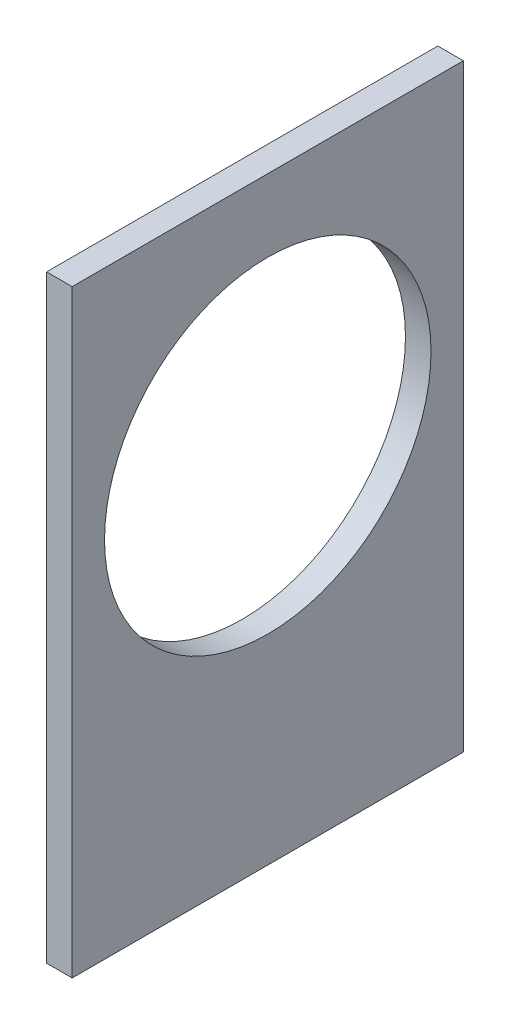
SolidWorks part; units mm, degrees
ref_plane "Front Plane" through (0, 0, 0) normal (0, 0, 1) x (1, 0, 0)
ref_plane "Top Plane" through (0, 0, 0) normal (0, 1, 0) x (1, 0, 0)
ref_plane "Right Plane" through (0, 0, 0) normal (1, 0, 0) x (0, 0, -1)
sketch "Sketch1" plane through (0, 0, 0) normal (1, 0, 0) x (0, 0, -1)
  line L1 (0, 0) -> (49, 0)
  line L2 (0, 0) -> (0, 75)
  line L3 (0, 75) -> (49, 75)
  line L4 (49, 0) -> (49, 75)
  dimension "D1" = 49
  dimension "D2" = 75
extrude "Boss-Extrude1" add sketch "Sketch1" along normal blind 3.2
sketch "Sketch2" plane through (3.2, 0, 0) normal (1, 0, 0) x (0, 0, -1)
  line L0 (24.5, 75) -> (24.5, 0) construction
  line L1 (49, 75) -> (0, 75) construction
  line L2 (0, 0) -> (49, 0) construction
  circle A0 centre (24.5, 45.4958) radius 20.445
  point P13 (24.5, 0)
  dimension "D1" = 20.445
extrude "Cut-Extrude1" cut sketch "Sketch2" against normal up to next
